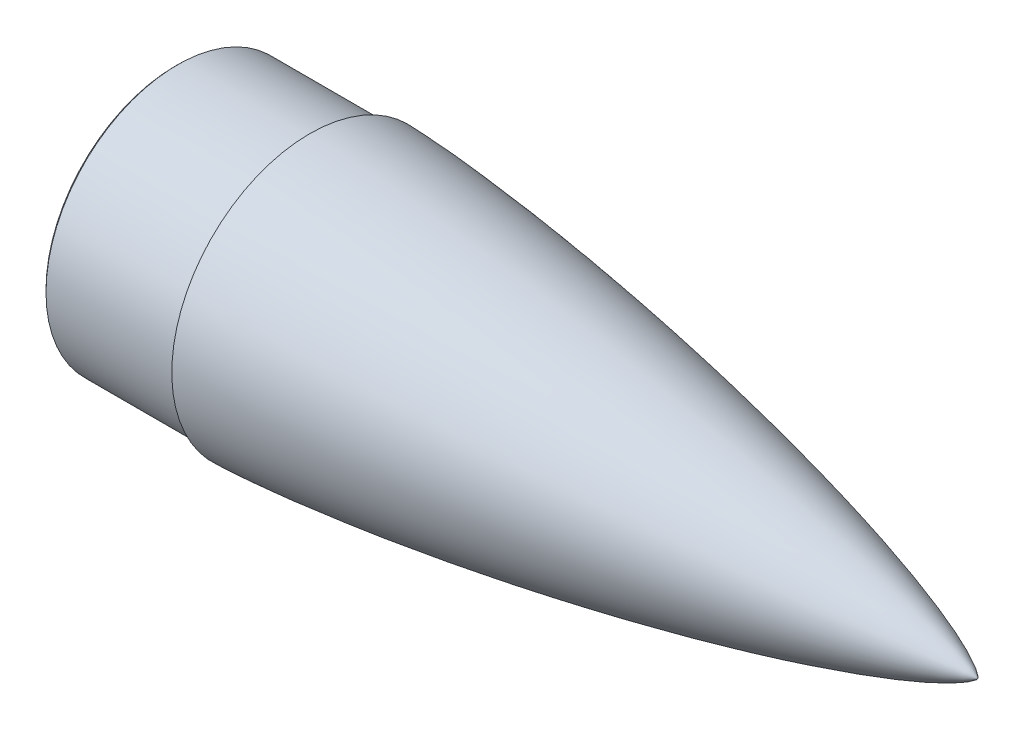
SolidWorks part; units mm, degrees
material "ABS"
ref_plane "Front Plane" through (0, 0, 0) normal (0, 0, 1) x (1, 0, 0)
ref_plane "Top Plane" through (0, 0, 0) normal (0, 1, 0) x (1, 0, 0)
ref_plane "Right Plane" through (0, 0, 0) normal (1, 0, 0) x (0, 0, -1)
ref_axis "Axis1" through (446.939, 0, 0) along (-1, 0, 0)
sketch "Sketch10" plane through (0, 0, 0) normal (0, 0, 1) x (1, 0, 0)
  line L1 (-0.5188, 0) -> (486.9547, 0) construction
  line L3 (10.6359, 77.55) -> (-82.1547, 77.55)
  line L4 (409.4812, 0) -> (369.4812, 0)
  line L5 (-82.1547, 77.55) -> (-82.1547, 80.55)
  line L6 (-82.1547, 80.55) -> (0.3953, 80.55)
  line L7 (0.3953, 80.55) -> (0.3953, 84.55)
  line L8 (446.939, 0) -> (-88.2629, 0) construction
  spline S0 degree 4 poles (409.4812, 0) (409.4788, 0.0135) (409.4718, 0.0399) (409.45, 0.0903) (409.4052, 0.1736) (409.3386, 0.2747) (409.2332, 0.4144) (409.0715, 0.6026) (408.8144, 0.8684) (408.376, 1.2687) (407.6237, 1.874) (406.3009, 2.8069) (403.9508, 4.2541) (399.8003, 6.4739) (392.937, 9.6599) (381.0889, 14.4581) (364.0279, 20.4397) (342.5658, 27.076) (317.7374, 33.9485) (292.1491, 40.4025) (266.444, 46.3727) (240.6453, 51.9227) (214.7673, 57.0897) (188.82, 61.8964) (166.0615, 65.7958) (146.5183, 68.9193) (130.2092, 71.3728) (117.1484, 73.2437) (104.0744, 75.0198) (92.6232, 76.4872) (82.7998, 77.6794) (74.6082, 78.627) (68.0516, 79.3563) (61.4918, 80.0556) (54.9286, 80.7233) (48.3622, 81.3575) (41.7923, 81.956) (36.0408, 82.4459) (31.1087, 82.8394) (26.9972, 83.1482) (23.7071, 83.3831) (20.0917, 83.6266) (16.7244, 83.837) (13.6055, 84.0163) (10.7352, 84.1667) (8.4384, 84.2771) (6.1411, 84.3768) (4.1305, 84.4519) (2.4068, 84.5068) (1.2575, 84.5344) (0.6827, 84.5468) (0.3953, 84.55) knots 0 0 0 0 0 0.00013 0.00026 0.00052 0.0009 0.00128 0.001925 0.002882 0.004418 0.006927 0.011111 0.018279 0.030673 0.051704 0.083102 0.139909 0.202703 0.265496 0.32829 0.391083 0.453877 0.516671 0.579464 0.642258 0.673655 0.705051 0.736448 0.767845 0.799242 0.81494 0.830639 0.846337 0.862036 0.877734 0.893432 0.909131 0.924829 0.932678 0.940527 0.948377 0.956226 0.967169 0.972641 0.978113 0.983585 0.989056 0.994528 0.997264 1 1 1 1 1 construction
  spline S1 degree 4 poles (409.4812, 0) (409.4788, 0.0135) (409.4718, 0.0399) (409.45, 0.0903) (409.4052, 0.1736) (409.3386, 0.2747) (409.2332, 0.4144) (409.0715, 0.6026) (408.8144, 0.8684) (408.376, 1.2687) (407.6237, 1.874) (406.3009, 2.8069) (403.9508, 4.2541) (399.8003, 6.4739) (392.937, 9.6599) (381.0889, 14.4581) (364.0279, 20.4397) (342.5658, 27.076) (317.7374, 33.9485) (292.1491, 40.4025) (266.444, 46.3727) (240.6453, 51.9227) (214.7673, 57.0897) (188.82, 61.8964) (166.0615, 65.7958) (146.5183, 68.9193) (130.2092, 71.3728) (117.1484, 73.2437) (104.0744, 75.0198) (92.6232, 76.4872) (82.7998, 77.6794) (74.6082, 78.627) (68.0516, 79.3563) (61.4918, 80.0556) (54.9286, 80.7233) (48.3622, 81.3575) (41.7923, 81.956) (36.0408, 82.4459) (31.1087, 82.8394) (26.9972, 83.1482) (23.7071, 83.3831) (20.0917, 83.6266) (16.7244, 83.837) (13.6055, 84.0163) (10.7352, 84.1667) (8.4384, 84.2771) (6.1411, 84.3768) (4.1305, 84.4519) (2.4068, 84.5068) (1.2575, 84.5344) (0.6827, 84.5468) (0.3953, 84.55) knots 0 0 0 0 0 0.00013 0.00026 0.00052 0.0009 0.00128 0.001925 0.002882 0.004418 0.006927 0.011111 0.018279 0.030673 0.051704 0.083102 0.139909 0.202703 0.265496 0.32829 0.391083 0.453877 0.516671 0.579464 0.642258 0.673655 0.705051 0.736448 0.767845 0.799242 0.81494 0.830639 0.846337 0.862036 0.877734 0.893432 0.909131 0.924829 0.932678 0.940527 0.948377 0.956226 0.967169 0.972641 0.978113 0.983585 0.989056 0.994528 0.997264 1 1 1 1 1
  spline S2 degree 4 poles (369.4812, 0) (369.4791, 0.0123) (369.473, 0.0364) (369.4536, 0.0826) (369.4143, 0.1579) (369.3564, 0.2487) (369.265, 0.3739) (369.1239, 0.544) (368.8971, 0.7864) (368.5083, 1.1529) (367.8374, 1.7096) (366.658, 2.5667) (364.558, 3.8992) (360.8656, 5.9342) (354.8053, 8.8368) (344.3912, 13.1972) (329.4315, 18.6326) (310.6283, 24.6697) (288.8649, 30.9351) (266.4273, 36.8293) (243.8806, 42.2906) (221.2463, 47.375) (198.5377, 52.1159) (175.764, 56.5332) (155.7855, 60.1229) (138.6272, 63.0029) (124.3068, 65.2683) (112.8377, 66.9981) (101.3561, 68.6423) (91.2987, 70.0029) (82.6704, 71.11) (75.4749, 71.9912) (69.7154, 72.6701) (63.9528, 73.322) (58.187, 73.9452) (52.418, 74.5383) (46.6458, 75.099) (41.5922, 75.5591) (37.2585, 75.9295) (33.6456, 76.2208) (30.7544, 76.4427) (27.6004, 76.6718) (24.1831, 76.9027) (20.9952, 77.0983) (18.0369, 77.2597) (15.5707, 77.3785) (13.844, 77.4512) (12.3636, 77.5052) (11.3764, 77.5333) (10.8827, 77.5462) (10.6359, 77.55) knots 0 0 0 0 0 0.000135 0.00027 0.00054 0.00092 0.001299 0.001947 0.002931 0.004512 0.007081 0.01138 0.018708 0.031424 0.052705 0.084103 0.14091 0.203703 0.266497 0.329291 0.392084 0.454878 0.517672 0.580465 0.643259 0.674656 0.706052 0.737449 0.768846 0.800243 0.815941 0.831639 0.847338 0.863036 0.878735 0.894433 0.910132 0.92583 0.933679 0.941528 0.949378 0.957227 0.96792 0.978613 0.98396 0.989307 0.994653 0.997327 1 1 1 1 1 construction
  spline S3 degree 4 poles (369.4812, 0) (369.4791, 0.0123) (369.473, 0.0364) (369.4536, 0.0826) (369.4143, 0.1579) (369.3564, 0.2487) (369.265, 0.3739) (369.1239, 0.544) (368.8971, 0.7864) (368.5083, 1.1529) (367.8374, 1.7096) (366.658, 2.5667) (364.558, 3.8992) (360.8656, 5.9342) (354.8053, 8.8368) (344.3912, 13.1972) (329.4315, 18.6326) (310.6283, 24.6697) (288.8649, 30.9351) (266.4273, 36.8293) (243.8806, 42.2906) (221.2463, 47.375) (198.5377, 52.1159) (175.764, 56.5332) (155.7855, 60.1229) (138.6272, 63.0029) (124.3068, 65.2683) (112.8377, 66.9981) (101.3561, 68.6423) (91.2987, 70.0029) (82.6704, 71.11) (75.4749, 71.9912) (69.7154, 72.6701) (63.9528, 73.322) (58.187, 73.9452) (52.418, 74.5383) (46.6458, 75.099) (41.5922, 75.5591) (37.2585, 75.9295) (33.6456, 76.2208) (30.7544, 76.4427) (27.6004, 76.6718) (24.1831, 76.9027) (20.9952, 77.0983) (18.0369, 77.2597) (15.5707, 77.3785) (13.844, 77.4512) (12.3636, 77.5052) (11.3764, 77.5333) (10.8827, 77.5462) (10.6359, 77.55) knots 0 0 0 0 0 0.000135 0.00027 0.00054 0.00092 0.001299 0.001947 0.002931 0.004512 0.007081 0.01138 0.018708 0.031424 0.052705 0.084103 0.14091 0.203703 0.266497 0.329291 0.392084 0.454878 0.517672 0.580465 0.643259 0.674656 0.706052 0.737449 0.768846 0.800243 0.815941 0.831639 0.847338 0.863036 0.878735 0.894433 0.910132 0.92583 0.933679 0.941528 0.949378 0.957227 0.96792 0.978613 0.98396 0.989307 0.994653 0.997327 1 1 1 1 1
  dimension "D4" = 80.55
  dimension "D1" = 84.55
  dimension "D3" = 410
  dimension "D5" = 370
  dimension "D6" = 82.55
  dimension "D2" = 3
revolve "Revolve1" add sketch "Sketch10" angle 360 about axis through (446.939, 0, 0) along (-1, 0, 0)
chamfer "Chamfer1" distance 1.5 angle 45 1 edges at (-82.1547, 0, -80.55)
equation "\"TubeDiameter\" = 6.500in"
equation "\"D1@Sketch10\"=(\"TubeDiameter\"/2)+2mm"
equation "\"D6@Sketch10\"=\"TubeDiameter\"/2"
equation "\"D4@Sketch10\"=\"TubeDiameter\"/2-2mm"
